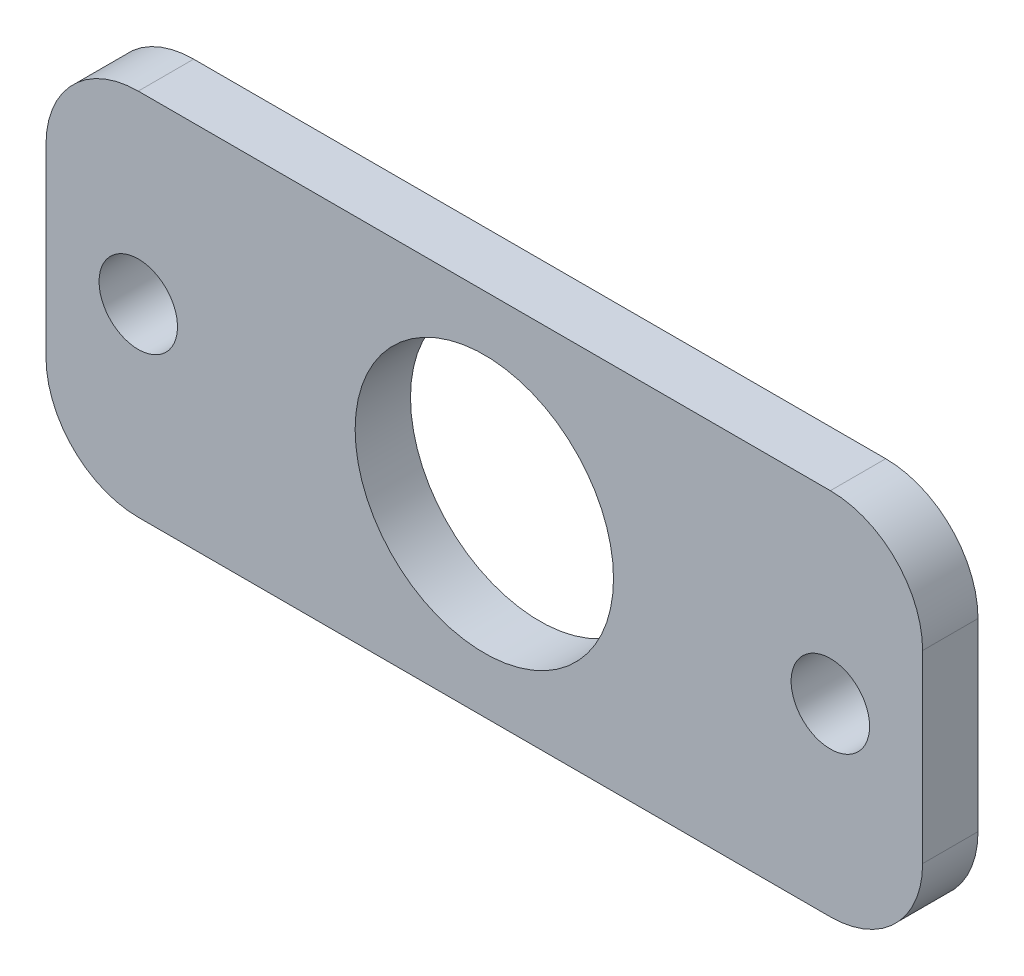
SolidWorks part; units mm, degrees
material "1.0553 (S355J0)"
ref_plane "Front Plane" through (0, 0, 0) normal (0, 0, 1) x (1, 0, 0)
ref_plane "Top Plane" through (0, 0, 0) normal (0, 1, 0) x (1, 0, 0)
ref_plane "Right Plane" through (0, 0, 0) normal (1, 0, 0) x (0, 0, -1)
sketch "Sketch1" plane through (0, 0, 0) normal (0, 0, 1) x (1, 0, 0)
  line L0 (-420, 0) -> (420, 0) construction
  line L1 (395, 0) -> (300, 0)
  line L2 (395, 0) -> (395, -40)
  line L3 (395, -40) -> (300, -40)
  line L4 (300, 0) -> (300, -40)
  line L5 (-420, -40) -> (420, -40) construction
  line L6 (347.5, -20) -> (395, -20) construction
  line L7 (347.5, -20) -> (347.5, -40) construction
  line L8 (395, 0) -> (395, 6) construction
  line L9 (300, 0) -> (300, 6) construction
  circle A0 centre (347.5, -20) radius 14
  circle A2 centre (347.5, -20) radius 8 construction
  circle A3 centre (385, -20) radius 4.25
  circle A4 centre (310, -20) radius 4.25
  dimension "D1" = 28
  dimension "D2" = 8.5
  dimension "D3" = 10
extrude "Boss-Extrude1" add sketch "Sketch1" along normal blind 6
fillet "Fillet1" radius 10 4 edges at (395, 0, 3) (395, -40, 3) (300, -40, 3) (300, 0, 3)
ref_plane "Plane1" through (347.5, 0, 0) normal (-1, 0, 0) x (0, 0, 1)
